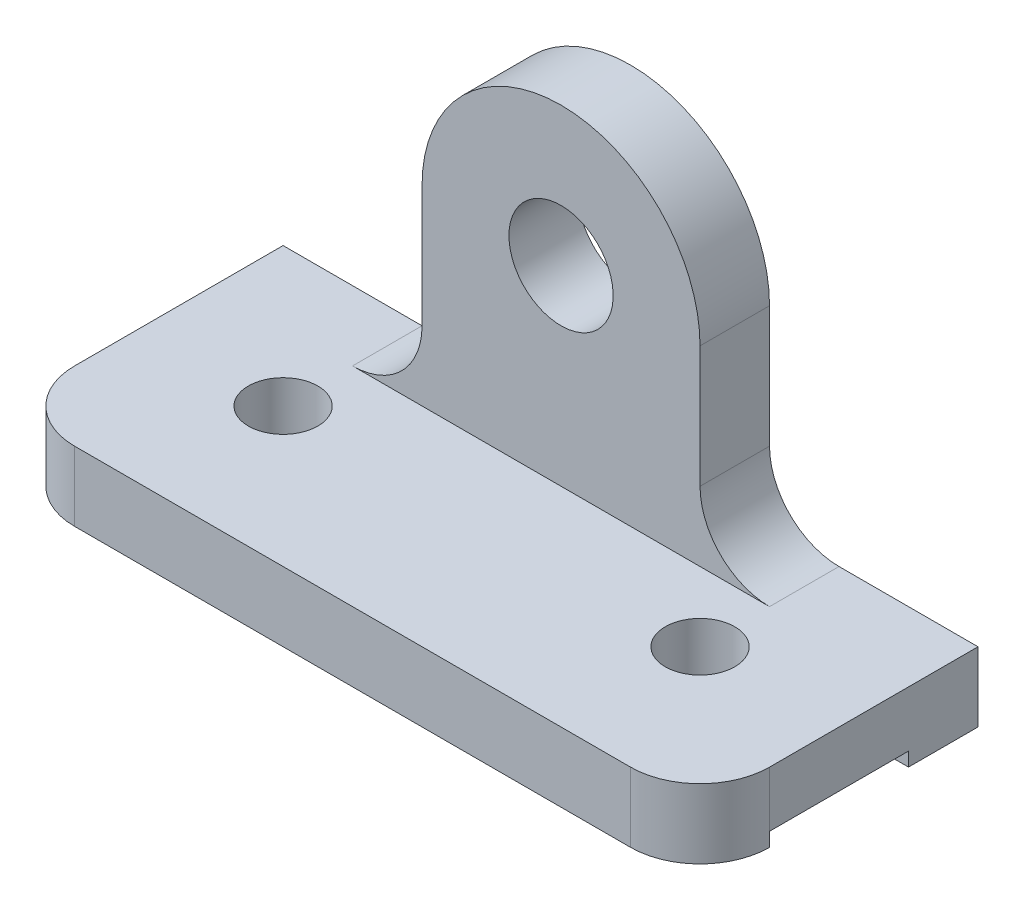
SolidWorks part; units mm, degrees
ref_plane "Alzado" through (0, 0, 0) normal (0, 0, 1) x (1, 0, 0)
ref_plane "Planta" through (0, 0, 0) normal (0, 1, 0) x (1, 0, 0)
ref_plane "Vista lateral" through (0, 0, 0) normal (1, 0, 0) x (0, 0, -1)
sketch "Croquis1" plane through (0, 0, 0) normal (1, 0, 0) x (0, 0, -1)
  line L1 (-20, 5) -> (20, 5)
  line L2 (-20, 5) -> (-20, -5)
  line L3 (-20, -5) -> (20, -5)
  line L4 (20, 5) -> (20, -5)
  line L5 (-20, 5) -> (20, -5) construction
  line L6 (-20, -5) -> (20, 5) construction
  point P0 (0, 0)
extrude "Saliente-Extruir1" add sketch "Croquis1" along normal blind 100
fillet "Redondeo2" radius 10 2 edges at (0, 0, 20) (100, 0, 20)
sketch "Croquis2" plane through (100, 0, 0) normal (1, 0, 0) x (0, 0, -1)
  line L1 (-10, -5) -> (20, -5) construction
  line L2 (10, -5) -> (10, -3)
  line L3 (10, -3) -> (-10, -3)
  line L4 (-10, -3) -> (-10, -5)
  line L5 (-10, -5) -> (10, -5)
extrude "Cortar-Extruir1" cut sketch "Croquis2" against normal blind 100
sketch "Croquis3" plane through (0, 5, 0) normal (0, 1, 0) x (1, 0, 0)
  circle A0 centre (20, 0) radius 5
  circle A1 centre (80, 0) radius 5
  dimension "D3" = 60
extrude "Cortar-Extruir2" cut sketch "Croquis3" against normal blind 10
sketch "Croquis5" plane through (0, 0, -20) normal (0, 0, -1) x (-1, 0, 0)
  line L0 (-70, 32.5) -> (-70, 15)
  line L1 (-80, 5) -> (-20, 5)
  line L2 (-100, 5) -> (0, 5) construction
  line L3 (-30, 32.5) -> (-30, 15)
  circle A0 centre (-50, 32.5) radius 7.5
  arc A1 (-30, 32.5) -> (-70, 32.5) centre (-50, 32.5) ccw
  arc A2 (-80, 5) -> (-70, 15) centre (-80, 15) ccw
  arc A3 (-20, 5) -> (-30, 15) centre (-20, 15) cw
  point P15 (-70, 5)
  point P18 (-30, 5)
  dimension "D1" = 10
  dimension "D2" = 10
extrude "Saliente-Extruir3" add sketch "Croquis5" against normal blind 10
